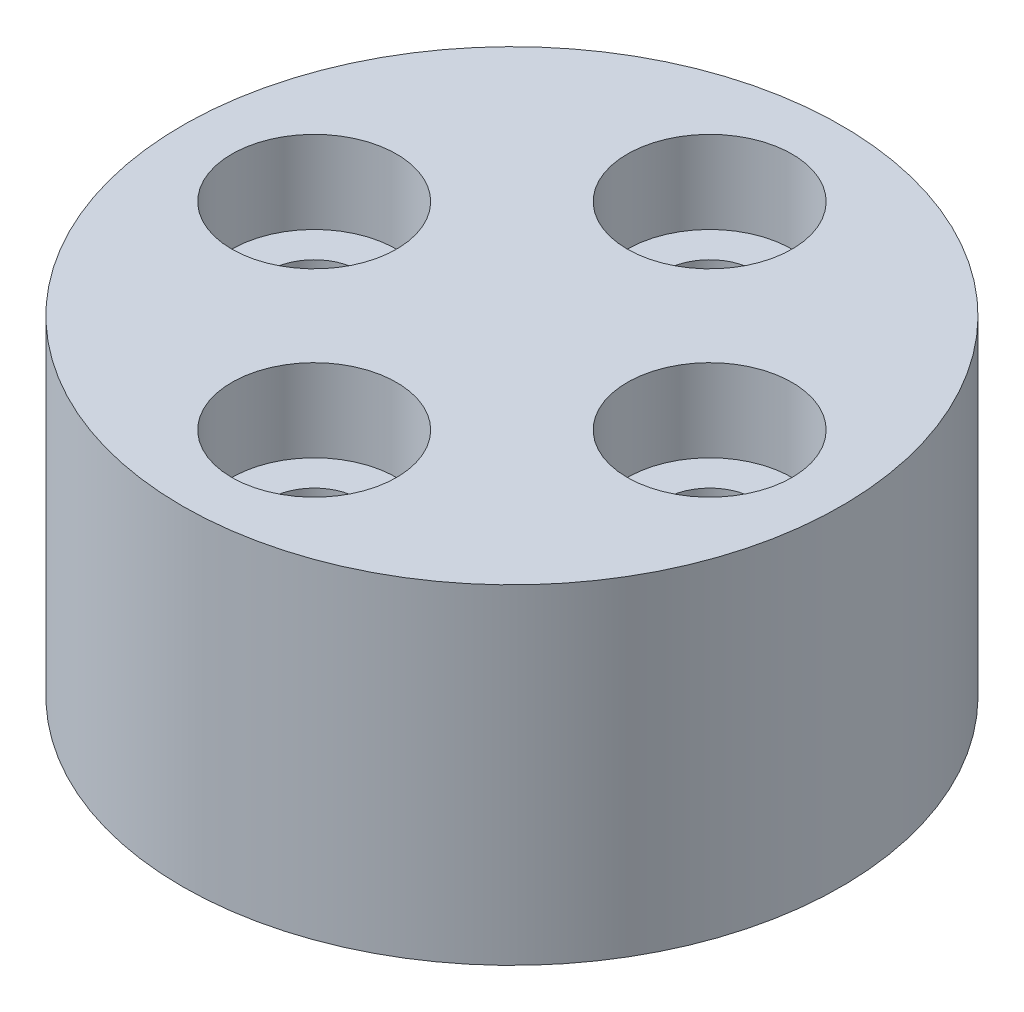
SolidWorks part; units mm, degrees
material "Plain Carbon Steel"
ref_plane "Front Plane" through (0, 0, 0) normal (0, 0, 1) x (1, 0, 0)
ref_plane "Top Plane" through (0, 0, 0) normal (0, 1, 0) x (1, 0, 0)
ref_plane "Right Plane" through (0, 0, 0) normal (1, 0, 0) x (0, 0, -1)
sketch "Sketch1" plane through (0, 0, 0) normal (0, 1, 0) x (1, 0, 0)
  circle A0 centre (0, 0) radius 20
  dimension "D1" = 40
extrude "Boss-Extrude1" add sketch "Sketch1" along normal blind 20
sketch "Sketch2" plane through (0, 20, 0) normal (0, 1, 0) x (1, 0, 0)
  line L0 (0, 20) -> (0, -20) construction
  line L1 (-20, 0) -> (20, 0) construction
  circle A0 centre (0, 0) radius 12
  circle A1 centre (0, 0) radius 20 construction
  dimension "D1" = 24
hole_wizard "CBORE for M5 Hex Head Bolt5" positions "3DSketch1" profile "Sketch3" counterbore size "M5" standard "ANSI Metric" end condition through all
sketch3d "3DSketch1"
  line L0 (0, 20, -20) -> (0, 20, 20) construction
  line L1 (-20, 20, 0) -> (20, 20, 0) construction
  circle A0 centre (0, 20, 0) radius 12 construction
  point P0 (0, 20, -12)
  point P4 (0, 32, 0)
  point P7 (12, 20, 0)
  point P11 (0, 20, 12)
  point P13 (-12, 20, 0)
sketch "Sketch3" plane through (0, 20, -12) normal (1, 0, 0) x (0, 0, 1)
  line L0 (0, 0) -> (0, 20)
  line L1 (0, 20) -> (2.75, 20)
  line L3 (2.75, 20) -> (2.75, 5)
  line L4 (2.75, 5) -> (5, 5)
  line L5 (5, 5) -> (5, 0)
  line L7 (5, 0) -> (0, 0)
  line L11 (0, -6.35) -> (0, 107.95) construction
  dimension "Thru Hole Dia." = 5.5
  dimension "Thru Hole Depth" = 20
  dimension "C'Bore Dia." = 10
  dimension "C'Bore Depth" = 5
ref_plane "Plane1" through (0, 20, 0) normal (0, 1, 0) x (1, 0, 0)
sketch "Sketch4" plane through (0, 20, 0) normal (0, 1, 0) x (1, 0, 0)
  circle A1 centre (0, 0) radius 20 construction
  circle A3 centre (0, 0) radius 20
